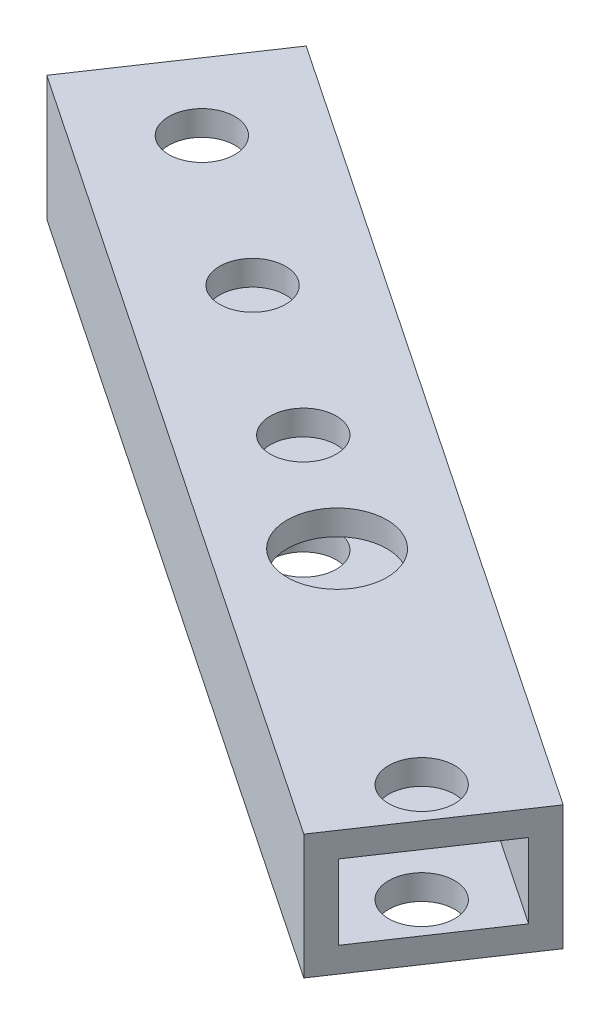
SolidWorks part; units mm, degrees
material "6061 合金"
ref_plane "前视基准面" through (0, 0, 0) normal (0, 0, 1) x (1, 0, 0)
ref_plane "上视基准面" through (0, 0, 0) normal (0, 1, 0) x (1, 0, 0)
ref_plane "右视基准面" through (0, 0, 0) normal (1, 0, 0) x (0, 0, -1)
sketch "草图1" plane through (0, 0, 0) normal (0, 1, 0) x (1, 0, 0)
  line L0 (0, 0) -> (275, 0) construction
  line L1 (0, 0) -> (0, 275) construction
  line L2 (0, 0) -> (194.4544, 194.4544) construction
  circle A0 centre (0, 0) radius 255
  circle A1 centre (0, 0) radius 275
  dimension "D1" = 510
  dimension "D2" = 20
  dimension "D3" = 45
extrude "凸台-拉伸1" add sketch "草图1" along normal blind 10
sketch "草图2" plane through (0, 10, 0) normal (0, 1, 0) x (1, 0, 0)
  line L0 (0, 0) -> (275, 0) construction
  line L1 (164.7559, 164.7559) -> (217.7889, 111.7229) construction
  line L2 (164.7559, 164.7559) -> (111.7229, 217.7889) construction
  line L3 (0, 0) -> (164.7559, 164.7559) construction
  line L4 (111.7229, 217.7889) -> (121.6224, 227.6884) construction
  line L5 (217.7889, 111.7229) -> (227.6884, 121.6224) construction
  line L6 (0, 0) -> (240.1716, 111.9938) construction
  line L7 (0, 0) -> (111.9938, 240.1716) construction
  line L8 (0, 0) -> (0, 275) construction
  line L9 (0, 185) -> (30, 185)
  line L10 (-110.5251, 257.2629) -> (-25.4233, 200)
  line L11 (111.9938, 240.1716) -> (30, 185)
  line L12 (0, 200) -> (-25.4233, 200)
  line L13 (240.1716, 111.9938) -> (185, 30)
  line L14 (185, 0) -> (185, 30)
  line L15 (-111.9938, 240.1716) -> (-30, 185)
  line L16 (0, 200) -> (25.4233, 200)
  line L17 (110.5251, 257.2629) -> (25.4233, 200)
  line L18 (257.2629, 110.5251) -> (200, 25.4233)
  line L19 (200, 0) -> (200, 25.4233)
  line L20 (0, 185) -> (-30, 185)
  line L21 (0, 185) -> (-30, 185) construction
  line L22 (0, 200) -> (-30, 200) construction
  line L23 (200, 0) -> (200, -1.5596) construction
  line L24 (185, 0) -> (185, -1.5596) construction
  line L25 (-200, -25.4233) -> (-200, 25.4233)
  line L26 (-257.2629, 110.5251) -> (-200, 25.4233)
  line L27 (-185, -30) -> (-185, 30)
  line L28 (-240.1716, 111.9938) -> (-185, 30)
  line L29 (185, 0) -> (185, -30)
  line L30 (200, 0) -> (200, -25.4233)
  line L31 (257.2629, -110.5251) -> (200, -25.4233)
  line L32 (240.1716, -111.9938) -> (185, -30)
  line L33 (164.7559, -164.7559) -> (111.7229, -217.7889) construction
  line L34 (110.5251, -257.2629) -> (25.4233, -200)
  line L35 (111.9938, -240.1716) -> (30, -185)
  line L36 (0, -185) -> (-30, -185)
  line L37 (0, -200) -> (-25.4233, -200)
  line L38 (0, -200) -> (25.4233, -200)
  line L39 (0, -185) -> (30, -185)
  line L40 (-111.9938, -240.1716) -> (-30, -185)
  line L41 (-110.5251, -257.2629) -> (-25.4233, -200)
  line L42 (-240.1716, -111.9938) -> (-185, -30)
  line L43 (-257.2629, -110.5251) -> (-200, -25.4233)
  circle A0 centre (0, 0) radius 275 construction
  arc A2 (111.9938, 240.1716) -> (240.1716, 111.9938) centre (0, 0) cw
  arc A3 (110.5251, 257.2629) -> (257.2629, 110.5251) centre (0, 0) cw
  arc A4 (-110.5251, 257.2629) -> (-257.2629, 110.5251) centre (0, 0) ccw
  arc A5 (-111.9938, 240.1716) -> (-240.1716, 111.9938) centre (0, 0) ccw
  arc A6 (110.5251, -257.2629) -> (257.2629, -110.5251) centre (0, 0) ccw
  arc A7 (111.9938, -240.1716) -> (240.1716, -111.9938) centre (0, 0) ccw
  arc A8 (-111.9938, -240.1716) -> (-240.1716, -111.9938) centre (0, 0) cw
  arc A9 (-110.5251, -257.2629) -> (-257.2629, -110.5251) centre (0, 0) cw
  point P60 (-185, 0)
  point P61 (-200, 0)
  dimension "D5" = 14
  dimension "D7" = 265
  dimension "D1" = 233
  dimension "D3" = 75
  dimension "D4" = 75
  dimension "D6" = 14
  dimension "D8" = 15
  dimension "D9" = 20
  dimension "D10" = 30
  dimension "D11" = 185
extrude "凸台-拉伸2" add sketch "草图2" along normal blind 10 separate body
sketch "草图8" plane through (0, 20, 0) normal (0, 1, 0) x (1, 0, 0)
  line L0 (0, 0) -> (-187.3833, 187.3833) construction
  line L1 (-243.7881, 137.7221) -> (-232.755, 126.689) construction
  line L2 (-137.7221, 243.7881) -> (-126.689, 232.755) construction
  line L3 (0, 0) -> (0, 200) construction
  line L4 (25.4233, 200) -> (-25.4233, 200) construction
  line L5 (-75, 233.3589) -> (-75, 215.2794) construction
  line L6 (75, 233.3589) -> (75, 215.2794) construction
  line L7 (-30, 185) -> (-111.9938, 240.1716) construction
  line L8 (-25.4233, 200) -> (-110.5251, 257.2629) construction
  line L9 (0, 0) -> (214.4019, 0) construction
  line L10 (200, -25.4233) -> (200, 25.4233) construction
  line L11 (-27.7116, 192.5) -> (-110.5251, 248.2231) construction
  line L12 (-10, 192.5) -> (-27.7116, 192.5) construction
  line L13 (-110.5251, 257.2629) -> (-110.5251, 248.2231) construction
  line L14 (-257.2629, 110.5251) -> (-248.2231, 110.5251) construction
  line L15 (-192.5, 27.7116) -> (-248.2231, 110.5251) construction
  line L16 (-233.3589, 75) -> (-215.2794, 75) construction
  line L17 (233.3589, 75) -> (215.2794, 75) construction
  line L18 (192.5, 27.7116) -> (248.2231, 110.5251) construction
  line L19 (257.2629, 110.5251) -> (248.2231, 110.5251) construction
  line L20 (243.7881, 137.7221) -> (232.755, 126.689) construction
  line L21 (137.7221, 243.7881) -> (126.689, 232.755) construction
  line L22 (0, 0) -> (187.3833, 187.3833) construction
  line L23 (110.5251, 257.2629) -> (110.5251, 248.2231) construction
  line L24 (27.7116, 192.5) -> (110.5251, 248.2231) construction
  line L25 (75, 233.3589) -> (75, 215.2794) construction
  line L26 (0, 185) -> (-20, 185) construction
  line L27 (30, 185) -> (-30, 185) construction
  line L28 (-20, 185) -> (-20, 200) construction
  line L29 (-25.4233, 200) -> (-20.6208, 196.7686) construction
  line L30 (-20.6208, 196.7686) -> (-28.9948, 184.3236) construction
  line L31 (-30, 185) -> (-28.9948, 184.3236) construction
  arc A0 (-111.9938, 240.1716) -> (-240.1716, 111.9938) centre (0, 0) ccw construction
  arc A1 (-110.5251, 257.2629) -> (-257.2629, 110.5251) centre (0, 0) ccw construction
  circle A2 centre (-10, 192.5) radius 2.65
  circle A3 centre (10, 192.5) radius 2.65
  circle A4 centre (-10, -192.5) radius 2.65
  circle A5 centre (10, -192.5) radius 2.65
  circle A6 centre (192.5, 10) radius 2.65
  circle A8 centre (192.5, -10) radius 2.65
  circle A9 centre (-192.5, 10) radius 2.65
  circle A10 centre (-192.5, -10) radius 2.65
  circle A11 centre (-110.5251, 248.2231) radius 1.65
  circle A12 centre (-27.7116, 192.5) radius 2.65
  circle A13 centre (-44.3049, 203.6652) radius 2.65 construction
  circle A14 centre (-56.7499, 212.0391) radius 2.65
  circle A15 centre (-69.1949, 220.413) radius 2.65
  circle A16 centre (-81.6399, 228.787) radius 2.65
  arc A17 (-238.2716, 132.2055) -> (-128.8116, 240.1233) centre (0, 0) cw construction
  circle A18 centre (-143.8082, 231.4538) radius 2.15
  circle A19 centre (-164.4155, 217.2997) radius 2.15
  circle A20 centre (-183.6389, 201.3166) radius 2.15
  circle A21 centre (-201.3166, 183.6389) radius 2.15
  circle A22 centre (-217.2997, 164.4155) radius 2.15
  circle A23 centre (-231.4538, 143.8082) radius 2.15
  circle A24 centre (-128.8116, 240.1233) radius 2.65
  circle A25 centre (-240.1233, 128.8116) radius 2.65
  circle A26 centre (-228.787, 81.6399) radius 2.65
  circle A27 centre (-220.413, 69.1949) radius 2.65
  circle A28 centre (-212.0391, 56.7499) radius 2.65
  circle A29 centre (-203.6652, 44.3049) radius 2.65
  circle A30 centre (-192.5, 27.7116) radius 2.65
  circle A31 centre (-248.2231, 110.5251) radius 1.65
  circle A32 centre (192.5, 27.7116) radius 2.65
  circle A33 centre (248.2231, 110.5251) radius 1.65
  circle A34 centre (203.6652, 44.3049) radius 2.65
  circle A35 centre (212.0391, 56.7499) radius 2.65
  circle A36 centre (220.413, 69.1949) radius 2.65
  circle A37 centre (228.787, 81.6399) radius 2.65
  circle A38 centre (240.1233, 128.8116) radius 2.65
  circle A39 centre (231.4538, 143.8082) radius 2.15
  arc A40 (238.2716, 132.2055) -> (128.8116, 240.1233) centre (0, 0) ccw construction
  circle A41 centre (128.8116, 240.1233) radius 2.65
  circle A42 centre (201.3166, 183.6389) radius 2.15
  circle A43 centre (183.6389, 201.3166) radius 2.15
  circle A44 centre (164.4155, 217.2997) radius 2.15
  circle A45 centre (143.8082, 231.4538) radius 2.15
  circle A46 centre (81.6399, 228.787) radius 2.65
  circle A47 centre (69.1949, 220.413) radius 2.65
  circle A48 centre (56.7499, 212.0391) radius 2.65
  circle A49 centre (44.3049, 203.6652) radius 2.65 construction
  circle A50 centre (110.5251, 248.2231) radius 1.65
  circle A51 centre (27.7116, 192.5) radius 2.65
  circle A52 centre (217.2997, 164.4155) radius 2.15
  dimension "D1" = 75
  dimension "D3" = 5.3
  dimension "D4" = 20
  dimension "D5" = 7.5
  dimension "D6" = 5.3
  dimension "D7" = 20
  dimension "D8" = 7.5
  dimension "D10" = 3.3
  dimension "D11" = 5.3
  dimension "D12" = 15
  dimension "D13" = 15
  dimension "D14" = 15
  dimension "D15" = 20
  dimension "D16" = 4.3
  dimension "D17" = 25
  dimension "D18" = 25
  dimension "D19" = 25
  dimension "D20" = 25
  dimension "D21" = 25
  dimension "D22" = 5.3
  dimension "D23" = 20
  dimension "D2" = 75
  dimension "D9" = 7.5
  dimension "D24" = 20
  dimension "D25" = 3.5
extrude "切除-拉伸1" cut sketch "草图8" against normal through all
sketch "草图9" plane through (0, 20, 0) normal (0, 1, 0) x (1, 0, 0)
  line L0 (-28.9948, 184.3236) -> (-20.6208, 196.7686)
  line L1 (-20.6208, 196.7686) -> (-83.6754, 239.1964)
  line L2 (-25.4233, 200) -> (-110.5251, 257.2629) construction
  line L3 (-83.6754, 239.1964) -> (-92.0493, 226.7514)
  line L4 (-30, 185) -> (-111.9938, 240.1716) construction
  line L5 (-92.0493, 226.7514) -> (-28.9948, 184.3236)
  dimension "D1" = 76
extrude "切除-拉伸2" cut sketch "草图9" against normal through all flip side to cut
sketch "草图10" plane through (0, 20, 0) normal (0, 1, 0) x (1, 0, 0)
  line L0 (-28.5396, 185) -> (-28.9948, 184.3236)
  line L1 (-28.9948, 184.3236) -> (-30, 185)
  line L2 (-30, 185) -> (-28.5396, 185)
  line L3 (-28.5396, 185) -> (-20.6208, 196.7686) construction
  line L4 (-30, 185) -> (-92.0493, 226.7514) construction
extrude "凸台-拉伸3" add sketch "草图10" against normal up to surface (10 mm away) up to face at (-56.7499, 10, -209.3891)
sketch "草图11" plane through (-105.3315, 0, -70.8749) normal (0.8297, 0, 0.5583) x (0.5583, 0, -0.8297)
  line L0 (136.7403, 20) -> (151.7403, 10) construction
  line L1 (151.7403, 20) -> (136.7403, 10) construction
  line L2 (151.7403, 10) -> (151.7403, 20) construction
  line L3 (138.7403, 12) -> (149.7403, 12)
  line L4 (138.7403, 12) -> (138.7403, 18)
  line L5 (138.7403, 18) -> (149.7403, 18)
  line L6 (149.7403, 12) -> (149.7403, 18)
  line L7 (138.7403, 12) -> (149.7403, 18) construction
  line L8 (138.7403, 18) -> (149.7403, 12) construction
  line L9 (136.7403, 20) -> (151.7403, 20) construction
  point P6 (144.2403, 15)
  dimension "D1" = 2
  dimension "D2" = 2
extrude "切除-拉伸3" cut sketch "草图11" against normal through all both and the other way through all
sketch "草图12" plane through (84.7107, 0, -125.8937) normal (0.5583, 0, -0.8297) x (-0.8297, 0, -0.5583)
  line L0 (275, 10) -> (-275, 10) construction
  line L1 (-342.4103, -10) -> (342.4103, -10)
  line L2 (-342.4103, -10) -> (-342.4103, 10)
  line L3 (-342.4103, 10) -> (342.4103, 10)
  line L4 (342.4103, -10) -> (342.4103, 10)
  line L5 (-342.4103, -10) -> (342.4103, 10) construction
  line L6 (-342.4103, 10) -> (342.4103, -10) construction
  point P0 (0, 0)
extrude "切除-拉伸4" cut sketch "草图12" against normal through all both and the other way through all
sketch "草图13" plane through (0, 10, 0) normal (0, -1, 0) x (1, 0, 0)
  circle A0 centre (-48.3019, -204.4363) radius 2.15
  circle A1 centre (-81.6399, -228.787) radius 2.65 construction
  dimension "D1" = 4.3
extrude "切除-拉伸5" [suppressed] cut sketch "草图13" against normal through all
sketch "草图14" plane through (0, 10, 0) normal (0, -1, 0) x (1, 0, 0)
  circle A0 centre (-47.5, -205.5) radius 4
  circle A1 centre (-56.7499, -212.0391) radius 2.65 construction
  dimension "D1" = 8
  dimension "D2" = 9.2499
  dimension "D3" = 6.5391
extrude "切除-拉伸6" cut sketch "草图14" against normal through all
sketch "草图15" plane through (0, 20, 0) normal (0, 1, 0) x (1, 0, 0)
  line L0 (-92.0493, 226.7514) -> (-104.4943, 235.1253)
  line L1 (-104.4943, 235.1253) -> (-96.1204, 247.5703)
  line L2 (-96.1204, 247.5703) -> (-83.6754, 239.1964)
  line L3 (-83.6754, 239.1964) -> (-92.0493, 226.7514)
  dimension "D1" = 15
